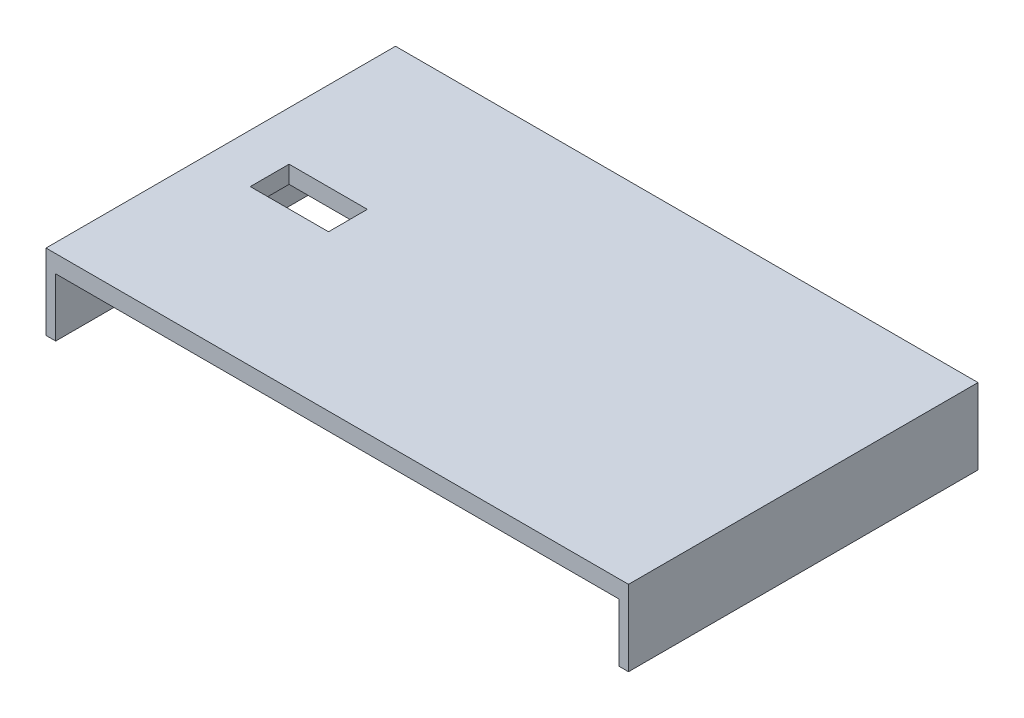
SolidWorks part; units mm, degrees
ref_plane "Front Plane" through (0, 0, 0) normal (0, 0, 1) x (1, 0, 0)
ref_plane "Top Plane" through (0, 0, 0) normal (0, 1, 0) x (1, 0, 0)
ref_plane "Right Plane" through (0, 0, 0) normal (1, 0, 0) x (0, 0, -1)
sketch "Sketch1" plane through (0, 0, 0) normal (0, 1, 0) x (1, 0, 0)
  line L1 (0, 0) -> (300, 0)
  line L2 (0, 0) -> (0, 180)
  line L3 (0, 180) -> (300, 180)
  line L4 (300, 0) -> (300, 180)
  point P5 (0, 0)
  dimension "D1" = 300
  dimension "D2" = 180
extrude "Boss-Extrude1" add sketch "Sketch1" along normal blind 9
sketch "Sketch2" plane through (0, 0, 0) normal (0, -1, 0) x (1, 0, 0)
  line L0 (0, 0) -> (300, 0) construction
  line L1 (0, -180) -> (5, -180)
  line L2 (0, -180) -> (0, 0)
  line L3 (0, 0) -> (5, 0)
  line L4 (5, -180) -> (5, 0)
  line L5 (300, -180) -> (0, -180) construction
  line L6 (300, 0) -> (295, 0)
  line L7 (300, 0) -> (300, -180)
  line L8 (300, -180) -> (295, -180)
  line L9 (295, 0) -> (295, -180)
  dimension "D1" = 5
  dimension "D2" = 5
extrude "Boss-Extrude2" add sketch "Sketch2" along normal blind 30
sketch "Sketch3" plane through (0, 9, 0) normal (0, 1, 0) x (1, 0, 0)
  line L0 (0, 0) -> (300, 0) construction
  line L1 (0, 180) -> (0, 0) construction
  line L3 (25.2, 80) -> (65.5, 80)
  line L4 (25.2, 80) -> (25.2, 100)
  line L5 (25.2, 100) -> (65.5, 100)
  line L6 (65.5, 80) -> (65.5, 100)
  circle A0 centre (55, 90) radius 38.5
  circle A1 centre (55, 90) radius 48.5
  circle A2 centre (55, 90) radius 28.5
  dimension "D1" = 77
  dimension "D8" = 97
  dimension "D9" = 57
  dimension "D2" = 90
  dimension "D3" = 55
  dimension "D4" = 10
  dimension "D5" = 29.8
  dimension "D6" = 40.3
  dimension "D7" = 20
extrude "Cut-Extrude1" cut sketch "Sketch3" against normal blind 9 contours L4 L3 L6 L5
